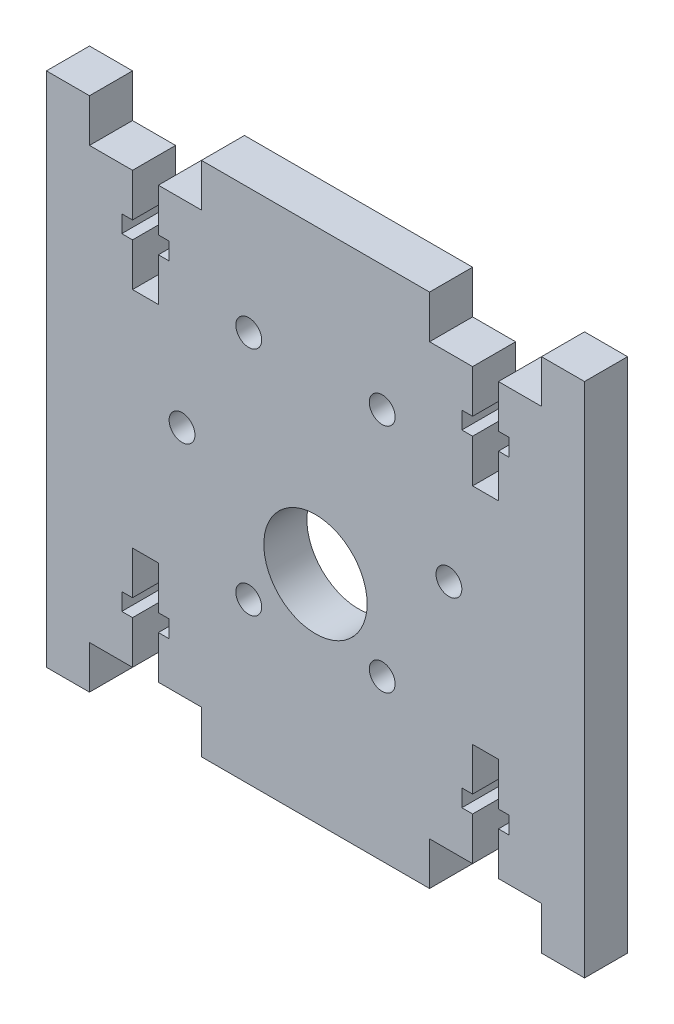
SolidWorks part; units mm, degrees
ref_plane "Front Plane" through (0, 0, 0) normal (0, 0, 1) x (1, 0, 0)
ref_plane "Top Plane" through (0, 0, 0) normal (0, 1, 0) x (1, 0, 0)
ref_plane "Right Plane" through (0, 0, 0) normal (1, 0, 0) x (0, 0, -1)
sketch "Sketch1" plane through (0, 0, 0) normal (0, 0, 1) x (1, 0, 0)
  line L1 (-27.5, -27) -> (27.5, -27)
  line L2 (-27.5, -27) -> (-27.5, 23)
  line L3 (-27.5, 23) -> (27.5, 23)
  line L4 (27.5, -27) -> (27.5, 23)
  line L5 (-27.5, -7) -> (27.5, -7) construction
  circle A2 centre (0, -7) radius 6
  circle A3 centre (0, 0) radius 15.5 construction
  circle A4 centre (-15.5, 0) radius 1.5
  circle A5 centre (-7.75, 13.4234) radius 1.5
  circle A6 centre (7.75, 13.4234) radius 1.5
  circle A7 centre (15.5, 0) radius 1.5
  circle A8 centre (7.75, -13.4234) radius 1.5
  circle A9 centre (-7.75, -13.4234) radius 1.5
  dimension "D1" = 12
  dimension "D5" = 3
  dimension "D8" = 31
  dimension "D2" = 55
  dimension "D3" = 50
  dimension "D6" = 20
  dimension "D7" = 7
  dimension "D4" = 6
extrude "Boss-Extrude1" add sketch "Sketch1" along normal blind 5
sketch "Sketch2" plane through (0, 0, 5) normal (0, 0, 1) x (1, 0, 0)
  line L0 (-27.5, -27) -> (27.5, -27) construction
  line L1 (-22.5, -20) -> (-17, -20)
  line L2 (-22.5, -20) -> (-22.5, -22)
  line L3 (-22.5, -22) -> (-17, -22)
  line L4 (-17, -20) -> (-17, -22)
  line L5 (-22.5, -20) -> (-17, -22) construction
  line L6 (-22.5, -22) -> (-17, -20) construction
  line L7 (17, -20) -> (22.5, -20)
  line L8 (17, -20) -> (17, -22)
  line L9 (17, -22) -> (22.5, -22)
  line L10 (22.5, -20) -> (22.5, -22)
  line L11 (17, -20) -> (22.5, -22) construction
  line L12 (17, -22) -> (22.5, -20) construction
  line L13 (-18.25, -15) -> (-21.25, -15)
  line L14 (-18.25, -15) -> (-18.25, -27)
  line L15 (-18.25, -27) -> (-21.25, -27)
  line L16 (-21.25, -15) -> (-21.25, -27)
  line L17 (-18.25, -15) -> (-21.25, -27) construction
  line L18 (-18.25, -27) -> (-21.25, -15) construction
  line L19 (-27.5, -2) -> (27.5, -2) construction
  line L20 (21.25, -15) -> (18.25, -15)
  line L21 (21.25, -15) -> (21.25, -27)
  line L22 (21.25, -27) -> (18.25, -27)
  line L23 (18.25, -15) -> (18.25, -27)
  line L24 (21.25, -15) -> (18.25, -27) construction
  line L25 (21.25, -27) -> (18.25, -15) construction
  line L26 (-27.5, 23) -> (-27.5, -27) construction
  line L27 (27.5, -27) -> (27.5, 23) construction
  line L28 (21.25, 23) -> (18.25, 11) construction
  line L29 (21.25, 11) -> (18.25, 23) construction
  line L30 (-18.25, 23) -> (-21.25, 11) construction
  line L31 (-18.25, 11) -> (-21.25, 23) construction
  line L32 (17, 18) -> (22.5, 16) construction
  line L33 (17, 16) -> (22.5, 18) construction
  line L34 (-22.5, 18) -> (-17, 16) construction
  line L35 (-22.5, 16) -> (-17, 18) construction
  line L36 (18.25, 11) -> (18.25, 23)
  line L37 (21.25, 23) -> (18.25, 23)
  line L38 (21.25, 11) -> (21.25, 23)
  line L39 (21.25, 11) -> (18.25, 11)
  line L40 (-21.25, 11) -> (-21.25, 23)
  line L41 (-18.25, 23) -> (-21.25, 23)
  line L42 (-18.25, 11) -> (-18.25, 23)
  line L43 (-18.25, 11) -> (-21.25, 11)
  line L44 (22.5, 16) -> (22.5, 18)
  line L45 (17, 18) -> (22.5, 18)
  line L46 (17, 16) -> (17, 18)
  line L47 (17, 16) -> (22.5, 16)
  line L48 (-17, 16) -> (-17, 18)
  line L49 (-22.5, 18) -> (-17, 18)
  line L50 (-22.5, 16) -> (-22.5, 18)
  line L51 (-22.5, 16) -> (-17, 16)
  point P0 (-19.75, -21)
  point P5 (19.75, -21)
  point P10 (-19.75, -21)
  point P17 (19.75, -21)
  point P44 (19.75, 17)
  point P45 (-19.75, 17)
  dimension "D1" = 5.5
  dimension "D2" = 2
  dimension "D3" = 5.5
  dimension "D4" = 2
  dimension "D5" = 3
  dimension "D6" = 3
  dimension "D7" = 12
  dimension "D8" = 12
  dimension "D9" = 5
  dimension "D10" = 5
extrude "Cut-Extrude1" cut sketch "Sketch2" against normal blind 5 contours L43 L40 L41 L42 | L48 L49 L50 L51 | L36 L37 L38 L39 | L46 L45 L44 L47 | L14 L15 L16 L13 | L4 L3 L2 L1 | L23 L22 L21 L20 | L8 L9 L10 L7
sketch "Sketch3" plane through (0, 0, 5) normal (0, 0, 1) x (1, 0, 0)
  line L0 (-18.25, -27) -> (18.25, -27) construction
  line L1 (-13.25, -27) -> (13.25, -27)
  line L2 (-13.25, -27) -> (-13.25, -32)
  line L3 (-13.25, -32) -> (13.25, -32)
  line L4 (13.25, -27) -> (13.25, -32)
  line L5 (-26.25, -29.5) -> (-13.25, -29.5) construction
  line L6 (-21.25, -22) -> (-21.25, -27) construction
  line L7 (21.25, -22) -> (21.25, -27) construction
  line L8 (26.25, -32) -> (31.25, -32)
  line L9 (26.25, -32) -> (26.25, 28)
  line L12 (27.5, -32) -> (26.25, -32)
  line L13 (26.25, -23.7445) -> (26.25, -32)
  line L14 (-19.75, -29.5) -> (-19.75, -15) construction
  line L15 (-18.25, -15) -> (-21.25, -15) construction
  line L16 (26.25, 28) -> (31.25, 28)
  line L17 (-21.25, 23) -> (-27.5, 23) construction
  line L18 (-26.25, -32) -> (-31.25, -32)
  line L19 (-26.25, -32) -> (-26.25, 28)
  line L20 (-26.25, 28) -> (-31.25, 28)
  line L21 (-31.25, -32) -> (-31.25, 28)
  line L22 (31.25, -32) -> (31.25, 28)
  line L23 (-27.5, -27) -> (-21.25, -27) construction
  line L24 (26.25, -29.5) -> (13.25, -29.5) construction
  line L25 (19.75, -29.5) -> (19.75, -15) construction
  line L26 (21.25, -15) -> (18.25, -15) construction
  line L27 (-26.25, -2) -> (26.25, -2) construction
  line L28 (13.25, 23) -> (13.25, 28)
  line L29 (-13.25, 28) -> (13.25, 28)
  line L30 (-13.25, 23) -> (-13.25, 28)
  line L31 (-13.25, 23) -> (13.25, 23)
  point P30 (-24.375, -27)
  dimension "D1" = 5
  dimension "D2" = 5
  dimension "D3" = 5
  dimension "D4" = 5
  dimension "D5" = 5
  dimension "D6" = 5
extrude "Boss-Extrude2" add sketch "Sketch3" against normal blind 5 contours L21 L18 L19 L20 | L4 L1 L2 L3 | L8 L22 L16 L9 | L30 L31 L28 L29
